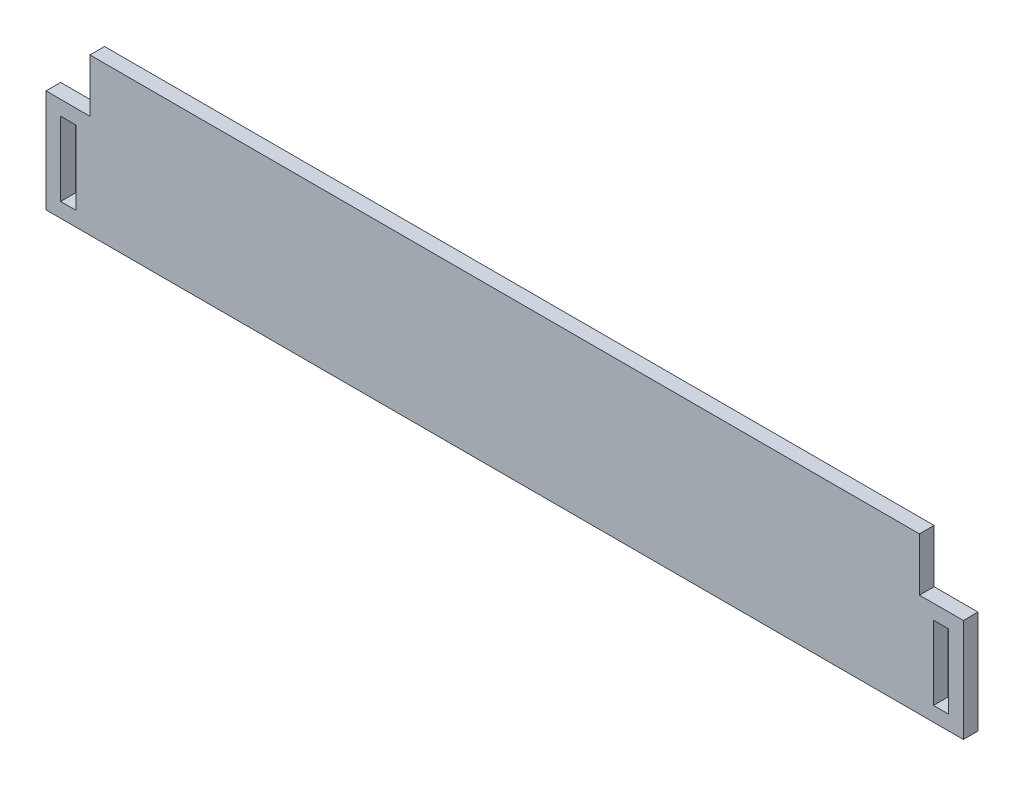
SolidWorks part; units mm, degrees
material "Pino"
ref_plane "Alzado" through (0, 0, 0) normal (0, 0, 1) x (1, 0, 0)
ref_plane "Planta" through (0, 0, 0) normal (0, 1, 0) x (1, 0, 0)
ref_plane "Vista lateral" through (0, 0, 0) normal (1, 0, 0) x (0, 0, -1)
sketch "Croquis1" plane through (0, 0, 0) normal (0, 0, 1) x (1, 0, 0)
  line L0 (-85, 21.123) -> (-94, 21.123)
  line L1 (85, 0) -> (-85, 0)
  line L2 (85, 0) -> (85, 32)
  line L3 (85, 32) -> (-85, 32)
  line L4 (-85, 0) -> (-85, 32)
  line L7 (-94, 21.123) -> (-94, 0)
  line L8 (-94, 0) -> (-85, 0)
  line L9 (0, 32) -> (0, 0) construction
  line L10 (87.877, 18.123) -> (87.877, 2.993)
  line L11 (-91, 18.123) -> (-87.877, 18.123)
  line L12 (-91, 18.123) -> (-91, 2.993)
  line L13 (-91, 2.993) -> (-87.877, 2.993)
  line L14 (-87.877, 18.123) -> (-87.877, 2.993)
  line L15 (91, 2.993) -> (87.877, 2.993)
  line L16 (91, 18.123) -> (91, 2.993)
  line L17 (91, 18.123) -> (87.877, 18.123)
  line L18 (94, 0) -> (85, 0)
  line L19 (94, 21.123) -> (94, 0)
  line L20 (85, 21.123) -> (94, 21.123)
  point P0 (0, 0)
extrude "Saliente-Extruir1" add sketch "Croquis1" along normal blind 3 contours L7 L8 L4 L0 L11 L14 L13 L12 | L9 L3 L4 L1 | L3 L9 L1 L2 | L20 L2 L18 L19 L17 L16 L15 L10
equation "\"mdf_wid\"= 3mm"
equation "\"mdf_hei\"= 15mm"
equation "\"alturagato\"= 110mm"
equation "\"separacion\"= 13mm"
equation "\"D1@Croquis1\"=\"mdf_hei\"+6+0.123"
equation "\"up\"= 80mm"
equation "\"down\"= 170mm"
equation "\"D2@Croquis1\"=\"down\""
equation "\"D3@Croquis1\"=\"up\"/2.5"
equation "\"D4@Croquis1\"=\"mdf_wid\"*3"
equation "\"D5@Croquis1\"=\"mdf_wid\""
equation "\"D6@Croquis1\"=\"mdf_wid\""
equation "\"D8@Croquis1\"=\"mdf_wid\"+0.123"
